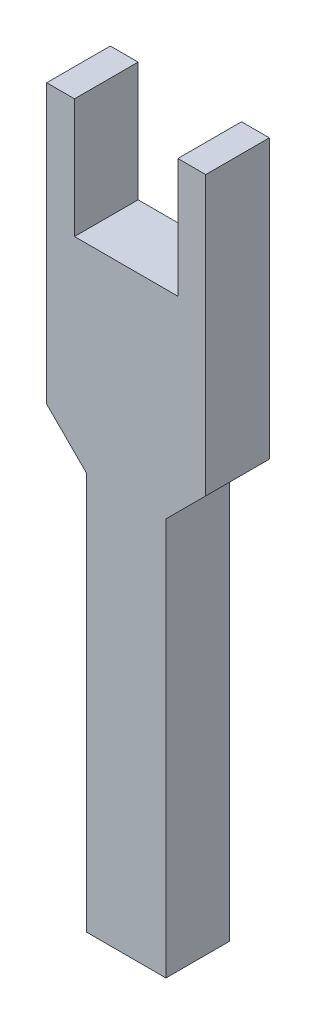
SolidWorks part; units mm, degrees
ref_plane "Alzado" through (0, 0, 0) normal (0, 0, 1) x (1, 0, 0)
ref_plane "Planta" through (0, 0, 0) normal (0, 1, 0) x (1, 0, 0)
ref_plane "Vista lateral" through (0, 0, 0) normal (1, 0, 0) x (0, 0, -1)
sketch "Croquis1" plane through (0, 0, 0) normal (0, 0, 1) x (1, 0, 0)
  line L1 (-10, 20) -> (10, 20)
  line L2 (-10, 20) -> (-10, -20)
  line L3 (-10, -20) -> (10, -20)
  line L4 (10, 20) -> (10, -20)
  line L5 (-10, 20) -> (10, -20) construction
  line L6 (-10, -20) -> (10, 20) construction
  point P0 (0, 0)
  dimension "D1" = 20
  dimension "D2" = 40
extrude "Saliente-Extruir1" add sketch "Croquis1" along normal blind 8
sketch "Croquis2" plane through (0, 0, 0) normal (0, 0, -1) x (-1, 0, 0)
  line L1 (-6.5, 20) -> (6.5, 20)
  line L2 (-6.5, 20) -> (-6.5, 5)
  line L3 (-6.5, 5) -> (6.5, 5)
  line L4 (6.5, 20) -> (6.5, 5)
  line L5 (-6.5, 20) -> (6.5, 5) construction
  line L6 (-6.5, 5) -> (6.5, 20) construction
  point P0 (0, 12.5)
extrude "Cortar-Extruir1" cut sketch "Croquis2" against normal blind 8
chamfer "Chaflán3" distance 5 angle 45 1 edges at (-10, -20, 4)
chamfer "Chaflán4" distance 5 angle 45 1 edges at (10, -20, 4)
sketch "Croquis4" plane through (0, -20, 0) normal (0, -1, 0) x (1, 0, 0)
  line L1 (5, 8) -> (-5, 8)
  line L2 (5, 8) -> (5, 0)
  line L3 (5, 0) -> (-5, 0)
  line L4 (-5, 8) -> (-5, 0)
extrude "Saliente-Extruir2" add sketch "Croquis4" along normal blind 50
